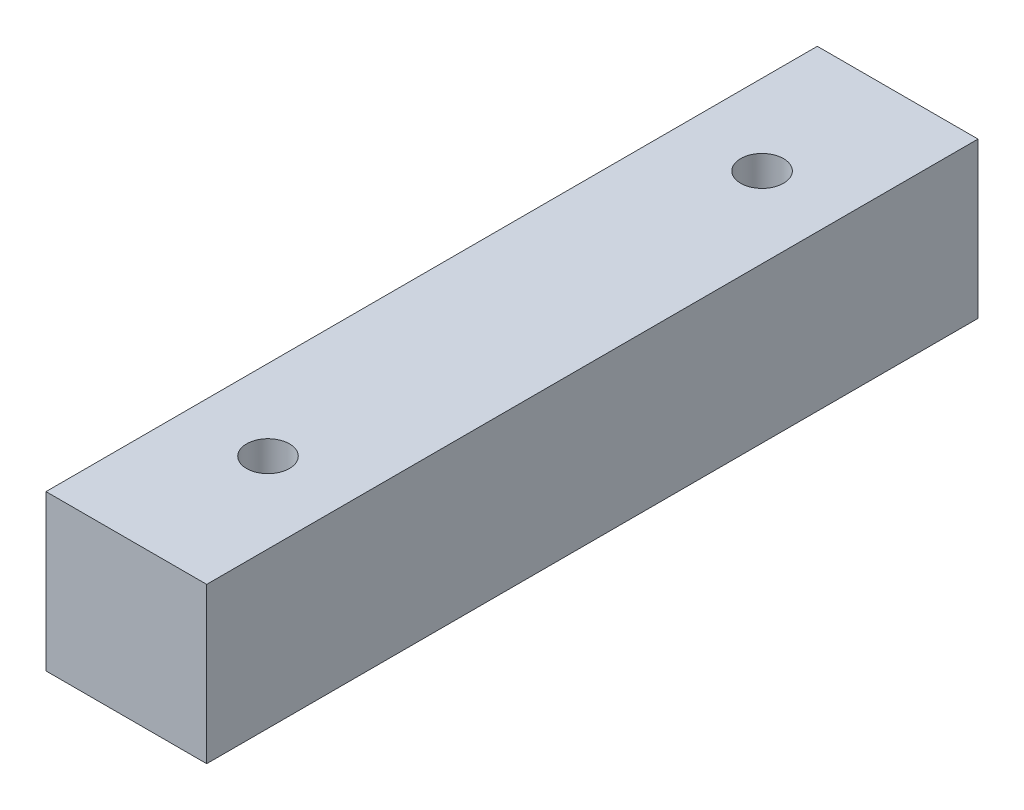
SolidWorks part; units mm, degrees
ref_plane "Front Plane" through (0, 0, 0) normal (0, 0, 1) x (1, 0, 0)
ref_plane "Top Plane" through (0, 0, 0) normal (0, 1, 0) x (1, 0, 0)
ref_plane "Right Plane" through (0, 0, 0) normal (1, 0, 0) x (0, 0, -1)
sketch "Sketch2" plane through (0, 0, 0) normal (1, 0, 0) x (0, 0, -1)
  line L1 (-6600, 1350) -> (6600, 1350)
  line L2 (-6600, 1350) -> (-6600, -1350)
  line L3 (-6600, -1350) -> (6600, -1350)
  line L4 (6600, 1350) -> (6600, -1350)
  line L5 (-6600, 1350) -> (6600, -1350) construction
  line L6 (-6600, -1350) -> (6600, 1350) construction
  point P0 (0, 0)
  dimension "D1" = 13200
  dimension "D2" = 2700
extrude "Boss-Extrude1" add sketch "Sketch2" along normal mid plane 3000
sketch "Sketch3" plane through (0, 0, 0) normal (1, 0, 0) x (0, 0, -1)
  line L0 (-4155.24, 1658.8484) -> (-4155.24, -299.5143)
  line L1 (-4155.24, -299.5143) -> (5068.7035, -299.5143)
  line L2 (5068.7035, -299.5143) -> (5068.7035, 1658.8484)
  line L3 (-6600, 1350) -> (-6600, -1350) construction
  dimension "D1" = 2444.76
ref_plane "Plane1" through (0, 1658.8484, 4155.24) normal (0, -1, 0) x (-1, 0, 0)
sketch "Sketch4" plane through (0, 1658.8484, 4155.24) normal (0, -1, 0) x (-1, 0, 0)
  line L0 (0, 0) -> (0, 9223.9435) construction
  circle A0 centre (0, 0) radius 400
  dimension "D1" = 800
sweep "Cut-Sweep1" cut profiles "Sketch4" path "Sketch3"
sketch "Sketch5" plane through (0, -1350, 0) normal (0, -1, 0) x (1, 0, 0)
  line L4 (-1500, 6600) -> (-1500, -6600)
  line L5 (-1500, -6600) -> (1500, -6600)
  line L6 (1500, -6600) -> (1500, 6600)
  line L7 (1500, 6600) -> (-1500, 6600)
  line L8 (-1500, 6600) -> (-1500, -6600)
  line L9 (-1500, -6600) -> (1500, -6600)
  line L10 (1500, -6600) -> (1500, 6600)
  line L11 (1500, 6600) -> (-1500, 6600)
  dimension "D1" = 0
extrude "Boss-Extrude2" add sketch "Sketch5" along normal blind 200
sketch "Sketch6" plane through (0, 0, 6600) normal (0, 0, 1) x (1, 0, 0)
  line L4 (-1500, 1350) -> (-1500, -1550)
  line L5 (-1500, -1550) -> (1500, -1550)
  line L6 (1500, -1550) -> (1500, 1350)
  line L7 (1500, 1350) -> (-1500, 1350)
  line L8 (-1500, 1350) -> (-1500, -1550)
  line L9 (-1500, -1550) -> (1500, -1550)
  line L10 (1500, -1550) -> (1500, 1350)
  line L11 (1500, 1350) -> (-1500, 1350)
  dimension "D1" = 0
extrude "Boss-Extrude3" add sketch "Sketch6" along normal blind 200
sketch "Sketch7" plane through (0, 0, -6600) normal (0, 0, -1) x (-1, 0, 0)
  line L4 (1500, -1550) -> (1500, 1350)
  line L5 (1500, 1350) -> (-1500, 1350)
  line L6 (-1500, 1350) -> (-1500, -1550)
  line L7 (-1500, -1550) -> (1500, -1550)
  line L8 (1500, -1550) -> (1500, 1350)
  line L9 (1500, 1350) -> (-1500, 1350)
  line L10 (-1500, 1350) -> (-1500, -1550)
  line L11 (-1500, -1550) -> (1500, -1550)
  dimension "D1" = 0
extrude "Boss-Extrude4" add sketch "Sketch7" along normal blind 1000
